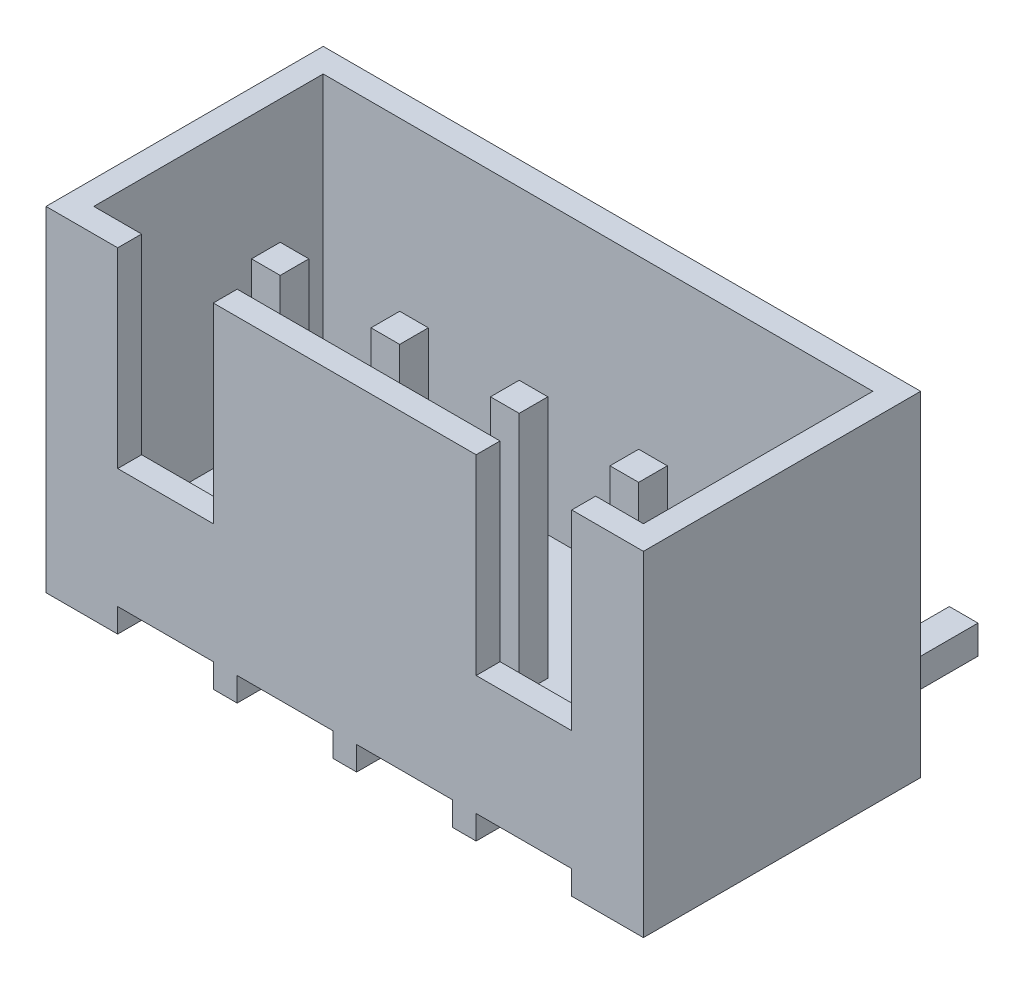
SolidWorks part; units mm, degrees
ref_plane "前视基准面" through (0, 0, 0) normal (0, 0, 1) x (1, 0, 0)
ref_plane "上视基准面" through (0, 0, 0) normal (0, 1, 0) x (1, 0, 0)
ref_plane "右视基准面" through (0, 0, 0) normal (1, 0, 0) x (0, 0, -1)
sketch "草图1" plane through (0, 0, 0) normal (0, 0, 1) x (1, 0, 0)
  line L0 (4, 0) -> (4, 0.5)
  line L1 (0, 0) -> (1.5, 0)
  line L2 (0, 0) -> (0, 7)
  line L3 (0, 7) -> (12.5, 7)
  line L4 (12.5, 0) -> (12.5, 7)
  line L5 (4, 0.5) -> (6, 0.5)
  line L6 (6, 0.5) -> (6, 0)
  line L7 (6.5, 0) -> (6.5, 0.5)
  line L8 (6.5, 0.5) -> (8.5, 0.5)
  line L9 (8.5, 0.5) -> (8.5, 0)
  line L10 (6, 0) -> (6.5, 0)
  line L11 (8.5, 0) -> (9, 0)
  line L12 (6.25, 4.6706) -> (6.25, 50004.6706) construction
  line L13 (3.75, 3.7509) -> (3.75, 50003.7509) construction
  line L14 (1.5, 0.5) -> (1.5, 0)
  line L15 (3.5, 0) -> (3.5, 0.5)
  line L16 (3.5, 0.5) -> (1.5, 0.5)
  line L17 (9, 0) -> (9, 0.5)
  line L18 (9, 0.5) -> (11, 0.5)
  line L19 (11, 0.5) -> (11, 0)
  line L20 (11, 0) -> (12.5, 0)
  line L21 (3.5, 0) -> (4, 0)
  dimension "D1" = 12.5
  dimension "D2" = 7
  dimension "D3" = 2.5
  dimension "D4" = 0.5
  dimension "D5" = 0.5
  dimension "D6" = 4
  dimension "D7" = 2.5
extrude "凸台-拉伸1" add sketch "草图1" along normal blind 5.8
sketch "草图2" plane through (0, 7, 0) normal (0, 1, 0) x (1, 0, 0)
  line L0 (0, -5.8) -> (0, 0) construction
  line L1 (0.5, -0.5) -> (12, -0.5)
  line L2 (0.5, -0.5) -> (0.5, -5.3)
  line L3 (0.5, -5.3) -> (12, -5.3)
  line L4 (12, -0.5) -> (12, -5.3)
  line L5 (12.5, 0) -> (0, 0) construction
  line L6 (12.5, -5.8) -> (12.5, 0) construction
  line L7 (12.5, -5.8) -> (0, -5.8) construction
  dimension "D1" = 0.5
  dimension "D2" = 0.5
  dimension "D3" = 0.5
  dimension "D4" = 0.5
extrude "切除-拉伸1" cut sketch "草图2" against normal blind 6
sketch "草图3" plane through (0, 0, 0) normal (0, -1, 0) x (1, 0, 0)
  line L0 (4, 0) -> (6, 0) construction
  line L1 (4.7, 3.7) -> (5.3, 3.7)
  line L2 (4.7, 3.7) -> (4.7, 3.1)
  line L3 (4.7, 3.1) -> (5.3, 3.1)
  line L4 (5.3, 3.7) -> (5.3, 3.1)
  line L5 (5, 4.7075) -> (5, 50004.7075) construction
  line L6 (4, 5.8) -> (4, 0) construction
  line L7 (6, 5.8) -> (6, 0) construction
  line L8 (6.25, 2.7254) -> (6.25, 50002.7254) construction
  line L9 (0, 5.8) -> (0, 0) construction
  line L10 (12.5, 5.8) -> (12.5, 0) construction
  line L11 (7.2, 3.7) -> (7.2, 3.1)
  line L12 (7.8, 3.1) -> (7.2, 3.1)
  line L13 (7.8, 3.7) -> (7.8, 3.1)
  line L14 (7.8, 3.7) -> (7.2, 3.7)
  line L15 (3.75, 0.9249) -> (3.75, -49999.0751) construction
  line L16 (2.8, 3.7) -> (2.8, 3.1)
  line L17 (2.2, 3.7) -> (2.2, 3.1)
  line L18 (2.8, 3.1) -> (2.2, 3.1)
  line L19 (2.8, 3.7) -> (2.2, 3.7)
  line L20 (9.7, 3.7) -> (9.7, 3.1)
  line L21 (9.7, 3.1) -> (10.3, 3.1)
  line L22 (10.3, 3.7) -> (10.3, 3.1)
  line L23 (9.7, 3.7) -> (10.3, 3.7)
  dimension "D1" = 0.6
  dimension "D2" = 3.1
  dimension "D3" = 2.5
  dimension "D4" = 2.5
extrude "凸台-拉伸2" add sketch "草图3" against normal blind 6.1
sketch "草图4" plane through (0, 0, 3.7) normal (0, 0, 1) x (1, 0, 0)
  line L0 (5.3, 0.5) -> (5.3, 0) construction
  line L1 (4.7, 0) -> (5.3, 0)
  line L2 (4.7, 0) -> (4.7, -0.6)
  line L3 (4.7, -0.6) -> (5.3, -0.6)
  line L4 (5.3, 0) -> (5.3, -0.6)
  line L5 (6.25, 1.7726) -> (6.25, 50001.7726) construction
  line L6 (0, 7) -> (0, 0) construction
  line L7 (12.5, 0) -> (12.5, 7) construction
  line L8 (7.2, 0) -> (7.2, -0.6)
  line L9 (7.8, -0.6) -> (7.2, -0.6)
  line L10 (7.8, 0) -> (7.8, -0.6)
  line L11 (7.8, 0) -> (7.2, 0)
  line L12 (3.75, 3.0585) -> (3.75, 50003.0585) construction
  line L13 (2.2, 0) -> (2.2, -0.6)
  line L14 (2.8, -0.6) -> (2.2, -0.6)
  line L15 (2.8, 0) -> (2.8, -0.6)
  line L16 (2.8, 0) -> (2.2, 0)
  line L17 (9.7, 0) -> (10.3, 0)
  line L18 (9.7, 0) -> (9.7, -0.6)
  line L19 (9.7, -0.6) -> (10.3, -0.6)
  line L20 (10.3, 0) -> (10.3, -0.6)
  dimension "D1" = 2.5
extrude "凸台-拉伸3" add sketch "草图4" against normal blind 7.1
sketch "草图5" plane through (0, 0, 5.8) normal (0, 0, 1) x (1, 0, 0)
  line L0 (0, 7) -> (0, 0) construction
  line L2 (1.5, 7) -> (1.5, 3)
  line L3 (12.5, 7) -> (0, 7) construction
  line L4 (1.5, 3) -> (3.5, 3)
  line L5 (11, 3) -> (11, 7)
  line L6 (1.5, 7) -> (3.5, 7)
  line L7 (12.5, 0) -> (12.5, 7) construction
  line L8 (3.5, 7) -> (3.5, 3)
  line L9 (9, 7) -> (9, 3)
  line L10 (9, 7) -> (11, 7)
  line L11 (9, 3) -> (11, 3)
  dimension "D1" = 1.5
  dimension "D2" = 1.5
  dimension "D3" = 4
  dimension "D4" = 2
  dimension "D5" = 2
extrude "切除-拉伸2" cut sketch "草图5" against normal blind 1
